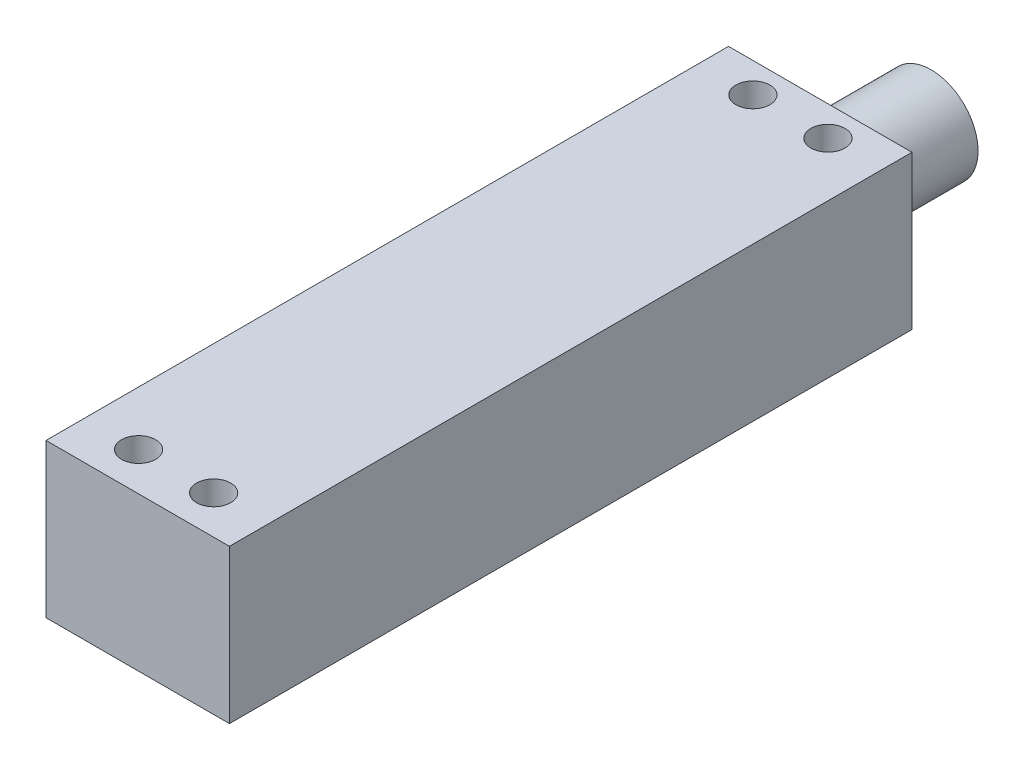
SolidWorks part; units mm, degrees
material "Chrome Stainless Steel"
ref_plane "Front Plane" through (0, 0, 0) normal (0, 0, 1) x (1, 0, 0)
ref_plane "Top Plane" through (0, 0, 0) normal (0, 1, 0) x (1, 0, 0)
ref_plane "Right Plane" through (0, 0, 0) normal (1, 0, 0) x (0, 0, -1)
ref_plane "Plane9" through (0, 10, 0) normal (0, 1, 0) x (1, 0, 0)
sketch "Sketch22" plane through (0, 0, 0) normal (0, 1, 0) x (1, 0, 0)
  line L5 (5.5, -119.3995) -> (-16, -199.3995) construction
  line L6 (5.5, -119.3995) -> (-16, -119.3995)
  line L7 (5.5, -119.3995) -> (5.5, -199.3995)
  line L8 (5.5, -199.3995) -> (-16, -199.3995)
  line L9 (-16, -119.3995) -> (-16, -199.3995)
  line L10 (-5.25, -199.3995) -> (-5.25, -119.3995) construction
  line L11 (5.5, -159.3995) -> (-16, -159.3995) construction
  point P4 (-5.25, -159.3995)
  point P6 (0, 0)
  dimension "D3" = 21.5
  dimension "D4" = 80
extrude "Boss-Extrude6" add sketch "Sketch22" along normal blind 18 from surface at 10 separate body starting at plane "Plane9"
sketch "Sketch23" plane through (0, 28, 0) normal (0, 1, 0) x (1, 0, 0)
  line L0 (-0.85, -194.8995) -> (-9.65, -194.8995) construction
  line L1 (-5.25, -122.8995) -> (-5.25, -195.8995) construction
  line L2 (4.7, -159.3995) -> (-15.2, -159.3995) construction
  line L3 (-0.85, -122.8995) -> (-9.65, -122.8995) construction
  line L5 (-9.65, -122.8995) -> (-9.65, -194.8995) construction
  line L6 (-0.85, -122.8995) -> (-0.85, -194.8995) construction
  line L7 (5.5, -199.3995) -> (-16, -199.3995) construction
  line L8 (-5.25, -122.8995) -> (-5.25, -119.3995) construction
  circle A0 centre (-9.65, -122.8995) radius 2
  circle A1 centre (-0.85, -122.8995) radius 2
  circle A2 centre (-0.85, -194.8995) radius 2
  circle A3 centre (-9.65, -194.8995) radius 2
  point P5 (-5.25, -195.8995)
  point P9 (-5.25, -122.8995)
  point P17 (-5.25, -159.3995)
  point P19 (-5.25, -159.3995)
  dimension "D2" = 4
  dimension "D3" = 4
  dimension "D7" = 4.5
  dimension "D1" = 73
  dimension "D4" = 72
  dimension "D5" = 4.4
  dimension "D6" = 4.4
extrude "Cut-Extrude9" cut sketch "Sketch23" against normal blind 4
sketch "Sketch24" plane through (0, 0, 119.3995) normal (0, 0, -1) x (-1, 0, 0)
  circle A2 centre (5.25, 19) radius 4
  circle A3 centre (5.25, 19) radius 5.5
  dimension "D1" = 11
extrude "Boss-Extrude7" add sketch "Sketch24" along normal blind 13
